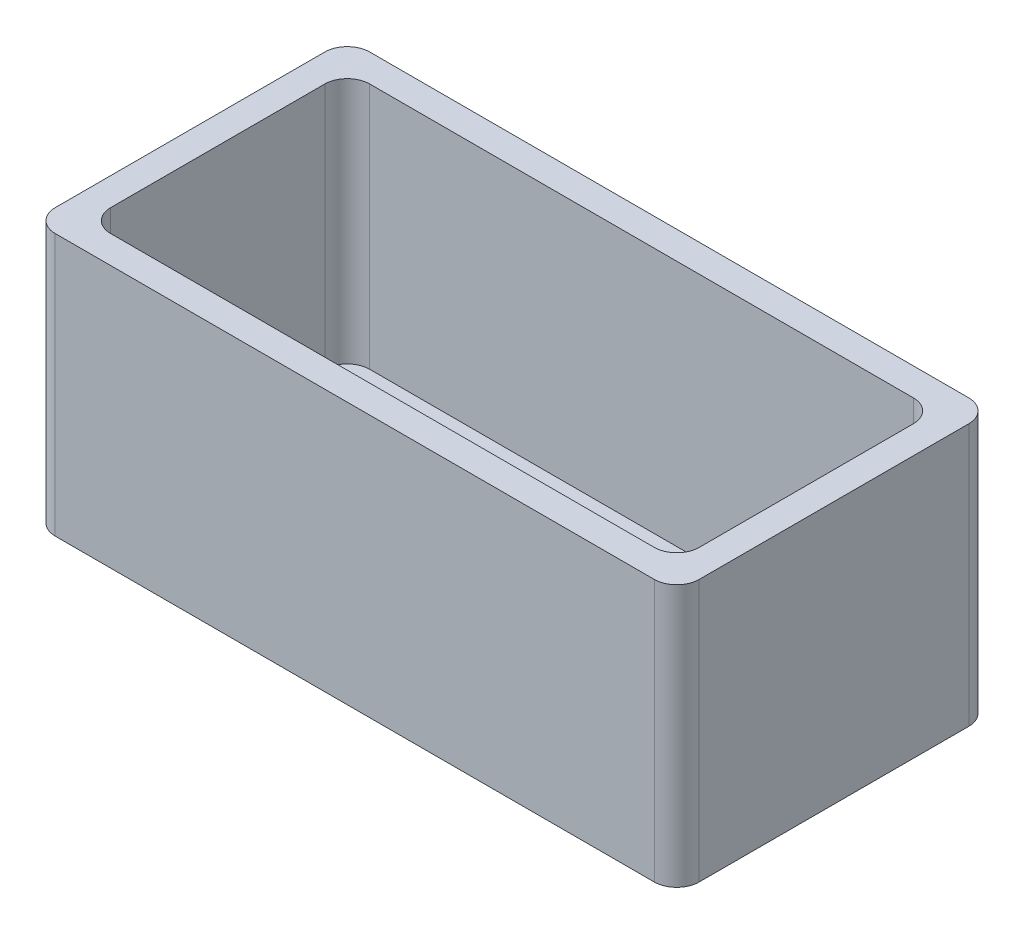
SolidWorks part; units mm, degrees
ref_plane "Front Plane" through (0, 0, 0) normal (0, 0, 1) x (1, 0, 0)
ref_plane "Top Plane" through (0, 0, 0) normal (0, 1, 0) x (1, 0, 0)
ref_plane "Right Plane" through (0, 0, 0) normal (1, 0, 0) x (0, 0, -1)
sketch "Sketch1" plane through (0, 0, 0) normal (0, 1, 0) x (1, 0, 0)
  line L0 (77, 10) -> (86, 10) construction
  line L1 (0, 0) -> (86, 0)
  line L2 (0, 0) -> (0, 42)
  line L3 (0, 42) -> (86, 42)
  line L4 (86, 0) -> (86, 42)
  line L5 (9, 10) -> (0, 10) construction
  circle A0 centre (9, 10) radius 1.5
  circle A1 centre (77, 10) radius 1.5
  dimension "D2" = 3
  dimension "D1" = 68
  dimension "D3" = 10
  dimension "D4" = 42
  dimension "D5" = 9
  dimension "D6" = 86
extrude "Boss-Extrude1" add sketch "Sketch1" along normal blind 35
fillet "Fillet1" radius 3 4 edges at (86, 17.5, 0) (86, 17.5, -42) (0, 17.5, -42) (0, 17.5, 0)
sketch "Sketch2" plane through (0, 35, 0) normal (0, 1, 0) x (1, 0, 0)
  line L24 (3.7, 3.7) -> (82.3, 3.7)
  line L25 (82.3, 3.7) -> (82.3, 38.3)
  line L26 (82.3, 38.3) -> (3.7, 38.3)
  line L27 (3.7, 38.3) -> (3.7, 3.7)
  line L28 (6.7, 3.7) -> (79.3, 3.7)
  line L29 (82.3, 6.7) -> (82.3, 35.3)
  line L30 (79.3, 38.3) -> (6.7, 38.3)
  line L31 (3.7, 35.3) -> (3.7, 6.7)
  arc A19 (6.7, 38.3) -> (3.7, 35.3) centre (6.7, 35.3) ccw
  arc A20 (6.7, 3.7) -> (3.7, 6.7) centre (6.7, 6.7) cw
  arc A21 (79.3, 3.7) -> (82.3, 6.7) centre (79.3, 6.7) ccw
  arc A22 (82.3, 35.3) -> (79.3, 38.3) centre (79.3, 35.3) ccw
  dimension "D2" = 3
  dimension "D1" = 3.7
extrude "Cut-Extrude1" cut sketch "Sketch2" against normal offset from surface (33 mm away) 2 up to face at (9, 0, -8.5)
